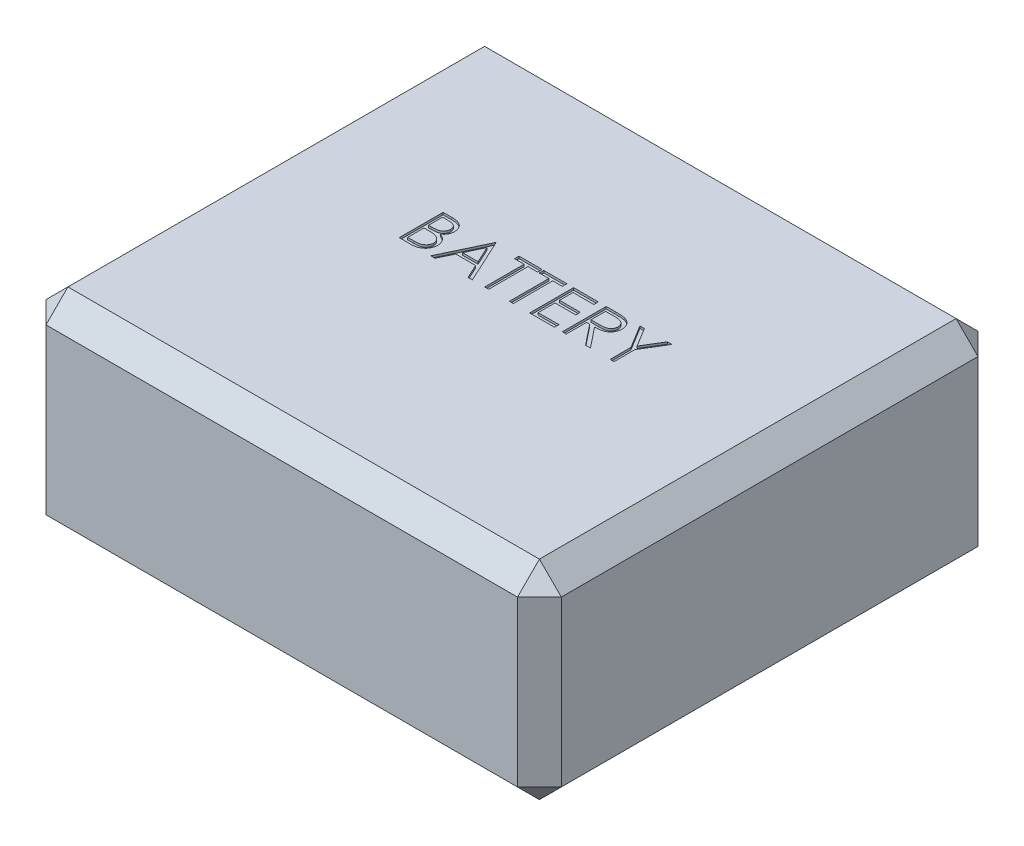
SolidWorks part; units mm, degrees
ref_plane "Front Plane" through (0, 0, 0) normal (0, 0, 1) x (1, 0, 0)
ref_plane "Top Plane" through (0, 0, 0) normal (0, 1, 0) x (1, 0, 0)
ref_plane "Right Plane" through (0, 0, 0) normal (1, 0, 0) x (0, 0, -1)
sketch "Sketch1" plane through (0, 0, 0) normal (0, 1, 0) x (1, 0, 0)
  line L1 (0, 0) -> (235, 0)
  line L2 (0, 0) -> (0, 210)
  line L3 (0, 210) -> (235, 210)
  line L4 (235, 0) -> (235, 210)
  dimension "D1" = 210
  dimension "D2" = 235
extrude "Boss-Extrude1" add sketch "Sketch1" along normal blind 95
sketch "Sketch2" plane through (0, 95, 0) normal (0, 1, 0) x (1, 0, 0)
  line L0 (0, 105) -> (235, 105) construction
  line L1 (0, 210) -> (0, 0) construction
  line L2 (235, 0) -> (235, 210) construction
  text T0 "BATTERY" font "Century Gothic" height 20
extrude "Cut-Extrude1" cut sketch "Sketch2" against normal blind 1
chamfer "Chamfer1" distance 10 angle 45 12 edges at (0, 95, -105) (0, 0, -105) (117.5, 95, -210) (0, 47.5, -210) (117.5, 0, -210) (235, 95, -105) (235, 47.5, -210) (235, 0, -105) (0, 47.5, 0) (117.5, 95, 0) (235, 47.5, 0) (117.5, 0, 0)
